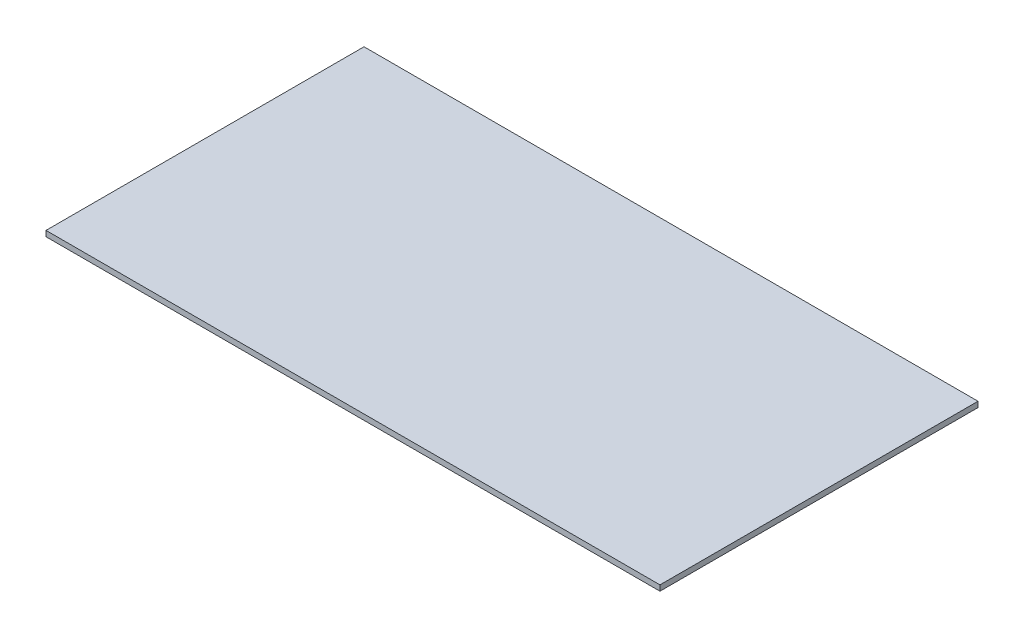
SolidWorks part; units mm, degrees
ref_plane "前视基准面" through (0, 0, 0) normal (0, 0, 1) x (1, 0, 0)
ref_plane "上视基准面" through (0, 0, 0) normal (0, 1, 0) x (1, 0, 0)
ref_plane "右视基准面" through (0, 0, 0) normal (1, 0, 0) x (0, 0, -1)
sketch "草图1" plane through (0, 0, 0) normal (0, 1, 0) x (1, 0, 0)
  line L1 (0, 0) -> (200, 0)
  line L2 (0, 0) -> (0, 103.6)
  line L3 (0, 103.6) -> (200, 103.6)
  line L4 (200, 0) -> (200, 103.6)
  dimension "D1" = 103.6
  dimension "D2" = 200
extrude "凸台-拉伸1" add sketch "草图1" along normal blind 1.8
